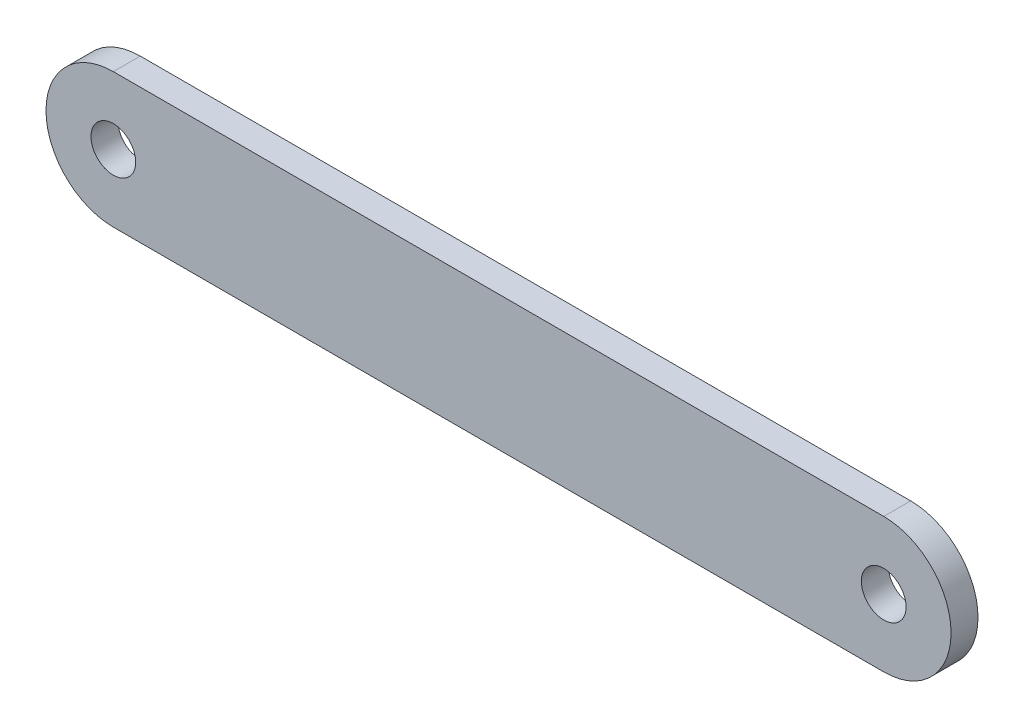
SolidWorks part; units mm, degrees
ref_plane "Přední rovina" through (0, 0, 0) normal (0, 0, 1) x (1, 0, 0)
ref_plane "Horní rovina" through (0, 0, 0) normal (0, 1, 0) x (1, 0, 0)
ref_plane "Pravá rovina" through (0, 0, 0) normal (1, 0, 0) x (0, 0, -1)
sketch "Skica1" plane through (0, 0, 0) normal (0, 0, 1) x (1, 0, 0)
  line L0 (0, 12.5) -> (143, 12.5)
  line L1 (0, -12.5) -> (143, -12.5)
  line L2 (0, 12.5) -> (0, -12.5) construction
  line L3 (143, -12.5) -> (143, 12.5) construction
  line L4 (-12.5, 0) -> (155.5, 0) construction
  arc A0 (0, 12.5) -> (0, -12.5) centre (0, 0) ccw
  arc A1 (143, 12.5) -> (143, -12.5) centre (143, 0) cw
  circle A2 centre (0, 0) radius 4.15
  circle A3 centre (143, 0) radius 4.15
  dimension "D3" = 8.3
  dimension "D4" = 8.3
  dimension "D1" = 25
  dimension "D2" = 143
extrude "Přidat vysunutím1" add sketch "Skica1" along normal blind 5
